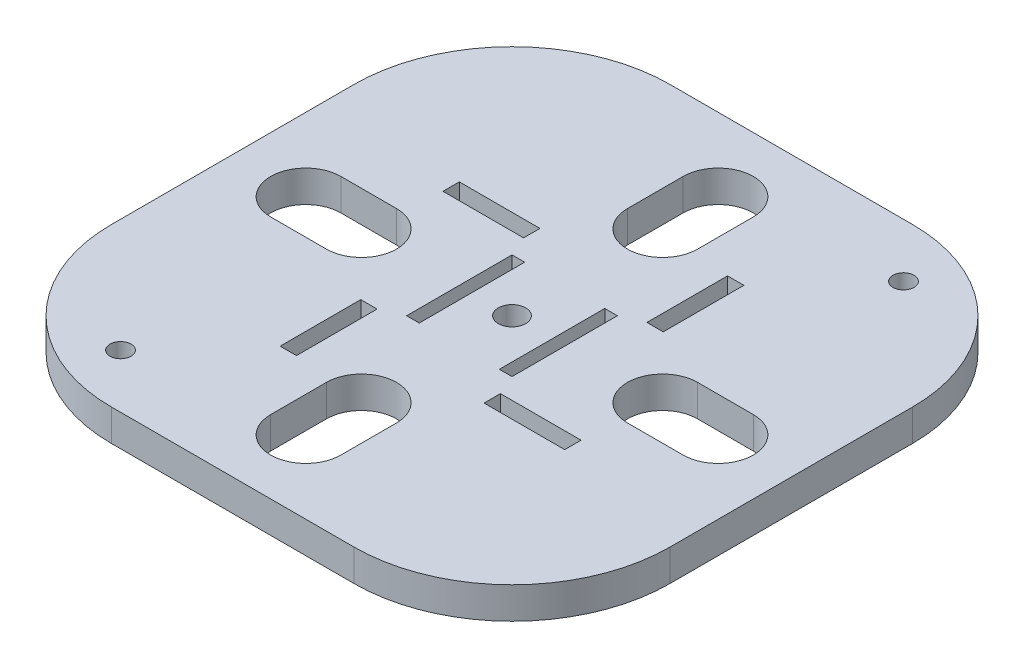
SolidWorks part; units mm, degrees
material "Acrílico (médio-alto impacto)"
ref_plane "Plano frontal" through (0, 0, 0) normal (0, 0, 1) x (1, 0, 0)
ref_plane "Plano superior" through (0, 0, 0) normal (0, 1, 0) x (1, 0, 0)
ref_plane "Plano direito" through (0, 0, 0) normal (1, 0, 0) x (0, 0, -1)
sketch "Esboço1" plane through (0, 0, 0) normal (0, 1, 0) x (1, 0, 0)
  line L1 (-26.5, -26.5) -> (26.5, -26.5)
  line L2 (-26.5, -26.5) -> (-26.5, 26.5)
  line L3 (-26.5, 26.5) -> (26.5, 26.5)
  line L4 (26.5, -26.5) -> (26.5, 26.5)
  line L5 (-26.5, -26.5) -> (26.5, 26.5) construction
  line L6 (-26.5, 26.5) -> (26.5, -26.5) construction
  point P0 (0, 0)
  dimension "D1" = 53
  dimension "D2" = 53
extrude "Ressalto-extrusão1" add sketch "Esboço1" along normal blind 3
sketch "Esboço3" plane through (0, 3, 0) normal (0, 1, 0) x (1, 0, 0)
  line L0 (-26.5, 26.5) -> (26.5, -26.5) construction
  line L1 (26.5, 26.5) -> (-26.5, -26.5) construction
  line B0 (-5, 0) -> (5, 0) construction
  line B1 (-5, 5) -> (-3.8, 5)
  line B2 (-5, 5) -> (-5, -5)
  line B3 (-5, -5) -> (-3.8, -5)
  line B4 (-3.8, 5) -> (-3.8, -5)
  line B5 (5, 5) -> (3.8, 5)
  line B6 (5, 5) -> (5, -5)
  line B7 (5, -5) -> (3.8, -5)
  line B8 (3.8, 5) -> (3.8, -5)
  circle B9 centre (0, 0) radius 1.3
sketch_block_instance "Bloco1-1"
sketch_block "Bloco1"
extrude "Corte-extrusão1" cut sketch "Esboço3" against normal through all
sketch "Esboço4" plane through (0, 3, 0) normal (0, 1, 0) x (-1, 0, 0)
  line L2 (-26.5, 26.5) -> (-26.5, -26.5) construction
  line L3 (-26.5, -26.5) -> (26.5, -26.5) construction
  line B0 (-6.95, -13.5) -> (-8.5, -13.5)
  line B1 (-6.95, -13.5) -> (-6.95, -5.85)
  line B2 (-6.95, -5.85) -> (-8.5, -5.85)
  line B3 (-8.5, -13.5) -> (-8.5, -5.85)
  line B4 (-13.5, 6.95) -> (-13.5, 8.5)
  line B5 (-13.5, 6.95) -> (-5.85, 6.95)
  line B6 (-5.85, 6.95) -> (-5.85, 8.5)
  line B7 (-13.5, 8.5) -> (-5.85, 8.5)
  line B8 (6.95, 13.5) -> (8.5, 13.5)
  line B9 (6.95, 13.5) -> (6.95, 5.85)
  line B10 (6.95, 5.85) -> (8.5, 5.85)
  line B11 (8.5, 13.5) -> (8.5, 5.85)
  line B12 (13.5, -6.95) -> (13.5, -8.5)
  line B13 (13.5, -6.95) -> (5.85, -6.95)
  line B14 (5.85, -6.95) -> (5.85, -8.5)
  line B15 (13.5, -8.5) -> (5.85, -8.5)
  dimension "D1" = 18
  dimension "D2" = 13
  dimension "D3" = 4
sketch_block_instance "Bloco2-1"
sketch_block "Bloco2" parameters "D1"=7.65, "D2"=1.55
sketch_block_instance "Bloco2-5"
sketch_block_instance "Bloco2-9"
sketch_block_instance "Bloco2-10"
sketch_block_instance "Bloco2-11"
extrude "Corte-extrusão2" cut sketch "Esboço4" against normal blind 10
fillet "Filete1" radius 15 4 edges at (-26.5, 1.5, -26.5) (-26.5, 1.5, 26.5) (26.5, 1.5, -26.5) (26.5, 1.5, 26.5)
sketch "Esboço5" plane through (0, 3, 0) normal (0, 1, 0) x (1, 0, 0)
  line L0 (19.5666, 0) -> (14.2835, 0) construction
  line L1 (19.5666, -3.3299) -> (14.2835, -3.3299)
  line L2 (19.5666, 3.3299) -> (14.2835, 3.3299)
  line L3 (0, 0) -> (26.5, 0) construction
  line L4 (0, -19.5666) -> (0, -14.2835) construction
  line L5 (-22.1066, -22.1066) -> (22.1066, 22.1066) construction
  line L6 (-22.1066, 22.1066) -> (22.1066, -22.1066) construction
  line L7 (-3.3299, -19.5666) -> (-3.3299, -14.2835)
  line L8 (-21.7828, -15.3594) -> (-14.5741, -22.568) construction
  line L9 (26.5, -11.5) -> (26.5, 11.5) construction
  line L10 (3.3299, -19.5666) -> (3.3299, -14.2835)
  line L11 (-19.5666, 0) -> (-14.2835, 0) construction
  line L12 (-19.5666, 3.3299) -> (-14.2835, 3.3299)
  line L13 (-19.5666, -3.3299) -> (-14.2835, -3.3299)
  line L14 (0, 19.5666) -> (0, 14.2835) construction
  line L15 (3.3299, 19.5666) -> (3.3299, 14.2835)
  line L16 (-3.3299, 19.5666) -> (-3.3299, 14.2835)
  arc A0 (19.5666, -3.3299) -> (19.5666, 3.3299) centre (19.5666, 0) ccw
  arc A1 (14.2835, 3.3299) -> (14.2835, -3.3299) centre (14.2835, 0) ccw
  arc A2 (-26.5, -11.5) -> (-11.5, -26.5) centre (-11.5, -11.5) ccw construction
  arc A3 (26.5, 11.5) -> (11.5, 26.5) centre (11.5, 11.5) ccw construction
  circle A4 centre (-15.7426, -21.3995) radius 1
  arc A5 (-11.5, 26.5) -> (-26.5, 11.5) centre (-11.5, 11.5) ccw construction
  arc A6 (11.5, -26.5) -> (26.5, -11.5) centre (11.5, -11.5) ccw construction
  circle A7 centre (15.7426, 21.3995) radius 1
  arc A8 (-3.3299, -19.5666) -> (3.3299, -19.5666) centre (0, -19.5666) ccw
  arc A9 (3.3299, -14.2835) -> (-3.3299, -14.2835) centre (0, -14.2835) ccw
  arc A10 (-19.5666, 3.3299) -> (-19.5666, -3.3299) centre (-19.5666, 0) ccw
  arc A11 (-14.2835, -3.3299) -> (-14.2835, 3.3299) centre (-14.2835, 0) ccw
  arc A12 (3.3299, 19.5666) -> (-3.3299, 19.5666) centre (0, 19.5666) ccw
  arc A13 (-3.3299, 14.2835) -> (3.3299, 14.2835) centre (0, 14.2835) ccw
  point P2 (16.9251, 0)
  point P39 (0, -16.9251)
  point P46 (-16.9251, 0)
  point P53 (0, 16.9251)
  dimension "D1" = 5
  dimension "D2" = 90
  dimension "D3" = 4
  dimension "D4" = 2
  dimension "D5" = 4
extrude "Corte-extrusão3" cut sketch "Esboço5" against normal through all
